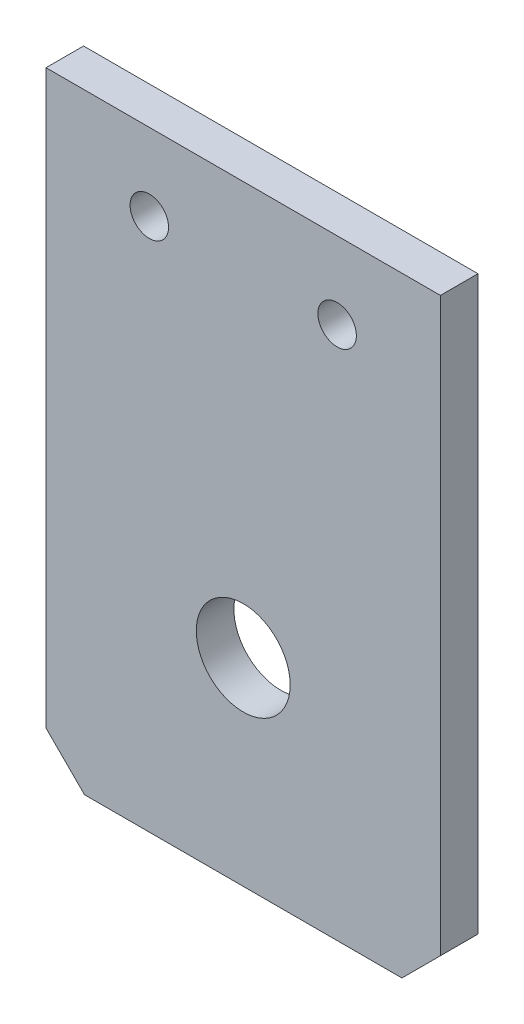
SolidWorks part; units mm, degrees
ref_plane "Alzado" through (0, 0, 0) normal (0, 0, 1) x (1, 0, 0)
ref_plane "Planta" through (0, 0, 0) normal (0, 1, 0) x (1, 0, 0)
ref_plane "Vista lateral" through (0, 0, 0) normal (1, 0, 0) x (0, 0, -1)
sketch "Croquis1" plane through (0, 0, 0) normal (0, 0, 1) x (1, 0, 0)
  line L0 (11, 56.8) -> (31, 56.8) construction
  line L1 (0, 65) -> (42, 65)
  line L2 (0, 65) -> (0, 0)
  line L3 (0, 0) -> (42, 0)
  line L4 (42, 65) -> (42, 0)
  line L5 (21, 56.8) -> (21, 21.08) construction
  line L6 (21, 65) -> (21, 56.8) construction
  line L7 (5.5, 36.58) -> (36.5, 5.58) construction
  line L8 (5.5, 5.58) -> (36.5, 36.58) construction
  circle A0 centre (11, 56.8) radius 2.05
  circle A1 centre (31, 56.8) radius 2.05
  circle A2 centre (5.5, 36.58) radius 1.575 construction
  circle A3 centre (36.5, 36.58) radius 1.575 construction
  circle A4 centre (36.5, 5.58) radius 1.575 construction
  circle A5 centre (5.5, 5.58) radius 1.575 construction
  circle A6 centre (21, 21.08) radius 11.5 construction
  dimension "D3" = 20
  dimension "D8" = 31
  dimension "D11" = 23
  dimension "D4" = 4.1
  dimension "D9" = 3.15
  dimension "D1" = 42
  dimension "D2" = 65
  dimension "D5" = 35.72
  dimension "D6" = 8.2
  dimension "D7" = 31
extrude "Saliente-Extruir1" add sketch "Croquis1" along normal blind 4
chamfer "Chaflán1" distance 4.1 angle 45 2 edges at (42, 0, 2) (0, 0, 2)
sketch "Croquis5" plane through (0, 0, 4) normal (0, 0, 1) x (1, 0, 0)
  line L0 (5.5, 5.58) -> (36.5, 36.58) construction
  circle A0 centre (21, 21.08) radius 5
  dimension "D1" = 10
extrude "Cortar-Extruir2" cut sketch "Croquis5" against normal through all
